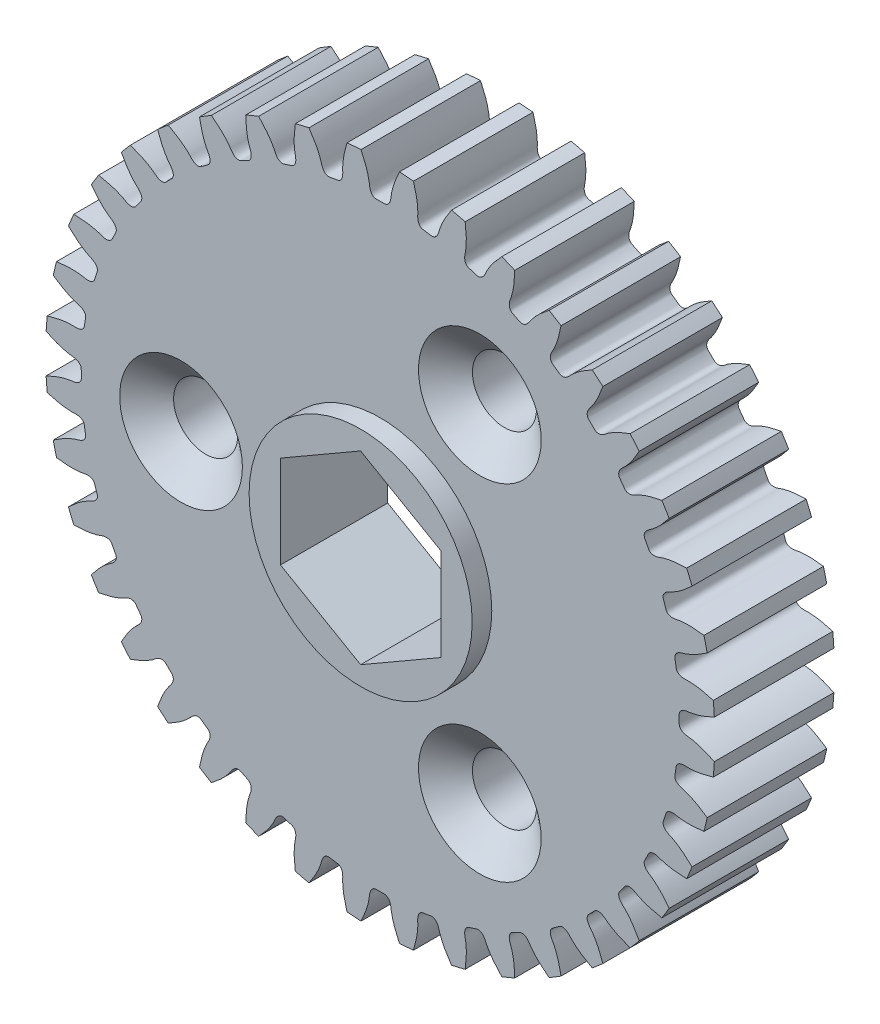
SolidWorks part; units mm, degrees
material "6061-T6 (SS)"
ref_plane "Front" through (0, 0, 0) normal (0, 0, 1) x (1, 0, 0)
ref_plane "Top" through (0, 0, 0) normal (0, 1, 0) x (1, 0, 0)
ref_plane "Side" through (0, 0, 0) normal (1, 0, 0) x (0, 0, -1)
ref_plane "Plane1" through (0, 0, -4.7625) normal (0, 0, -1) x (-1, 0, 0)
sketch "Sketch1" plane through (0, 0, -4.7625) normal (0, 0, -1) x (-1, 0, 0)
  arc A0 (-25.7968, 6.7684) -> (-26.058, 5.6808) centre (0, 0) ccw
  arc A1 (-26.5381, 2.6496) -> (-26.6258, 1.5345) centre (0, 0) ccw
  arc A2 (-26.6258, -1.5345) -> (-26.5381, -2.6496) centre (0, 0) ccw
  arc A3 (-26.058, -5.6808) -> (-25.7968, -6.7684) centre (0, 0) ccw
  arc A4 (-24.8485, -9.6872) -> (-24.4204, -10.7206) centre (0, 0) ccw
  arc A5 (-23.0271, -13.4551) -> (-22.4427, -14.4088) centre (0, 0) ccw
  arc A6 (-20.6388, -16.8917) -> (-19.9124, -17.7422) centre (0, 0) ccw
  arc A7 (-17.7422, -19.9124) -> (-16.8917, -20.6388) centre (0, 0) ccw
  arc A8 (-14.4088, -22.4427) -> (-13.4551, -23.0271) centre (0, 0) ccw
  arc A9 (-10.7206, -24.4204) -> (-9.6872, -24.8485) centre (0, 0) ccw
  arc A10 (-6.7684, -25.7968) -> (-5.6808, -26.058) centre (0, 0) ccw
  arc A11 (-2.6496, -26.5381) -> (-1.5345, -26.6258) centre (0, 0) ccw
  arc A12 (1.5345, -26.6258) -> (2.6496, -26.5381) centre (0, 0) ccw
  arc A13 (5.6808, -26.058) -> (6.7684, -25.7968) centre (0, 0) ccw
  arc A14 (9.6872, -24.8485) -> (10.7206, -24.4204) centre (0, 0) ccw
  arc A15 (13.4551, -23.0271) -> (14.4088, -22.4427) centre (0, 0) ccw
  arc A16 (16.8917, -20.6388) -> (17.7422, -19.9124) centre (0, 0) ccw
  arc A17 (19.9124, -17.7422) -> (20.6388, -16.8917) centre (0, 0) ccw
  arc A18 (22.4427, -14.4088) -> (23.0271, -13.4551) centre (0, 0) ccw
  arc A19 (24.4204, -10.7206) -> (24.8485, -9.6872) centre (0, 0) ccw
  arc A20 (25.7968, -6.7684) -> (26.058, -5.6808) centre (0, 0) ccw
  arc A21 (26.5381, -2.6496) -> (26.6258, -1.5345) centre (0, 0) ccw
  arc A22 (26.6258, 1.5345) -> (26.5381, 2.6496) centre (0, 0) ccw
  arc A23 (26.058, 5.6808) -> (25.7968, 6.7684) centre (0, 0) ccw
  arc A24 (24.8485, 9.6872) -> (24.4204, 10.7206) centre (0, 0) ccw
  arc A25 (23.0271, 13.4551) -> (22.4427, 14.4088) centre (0, 0) ccw
  arc A26 (20.6388, 16.8917) -> (19.9124, 17.7422) centre (0, 0) ccw
  arc A27 (17.7422, 19.9124) -> (16.8917, 20.6388) centre (0, 0) ccw
  arc A28 (14.4088, 22.4427) -> (13.4551, 23.0271) centre (0, 0) ccw
  arc A29 (10.7206, 24.4204) -> (9.6872, 24.8485) centre (0, 0) ccw
  arc A30 (6.7684, 25.7968) -> (5.6808, 26.058) centre (0, 0) ccw
  arc A31 (2.6496, 26.5381) -> (1.5345, 26.6258) centre (0, 0) ccw
  arc A32 (-1.5345, 26.6258) -> (-2.6496, 26.5381) centre (0, 0) ccw
  arc A33 (-5.6808, 26.058) -> (-6.7684, 25.7968) centre (0, 0) ccw
  arc A34 (-9.6872, 24.8485) -> (-10.7206, 24.4204) centre (0, 0) ccw
  arc A35 (-13.4551, 23.0271) -> (-14.4088, 22.4427) centre (0, 0) ccw
  arc A36 (-16.8917, 20.6388) -> (-17.7422, 19.9124) centre (0, 0) ccw
  arc A37 (-19.9124, 17.7422) -> (-20.6388, 16.8917) centre (0, 0) ccw
  arc A38 (-22.4427, 14.4088) -> (-23.0271, 13.4551) centre (0, 0) ccw
  arc A39 (-24.4204, 10.7206) -> (-24.8485, 9.6872) centre (0, 0) ccw
  spline S0 degree 3 number of poles 87 (-25.7968, 6.7684) -> (-24.8485, 9.6872)
  spline S1 degree 3 number of poles 87 (-26.5381, 2.6496) -> (-26.058, 5.6808)
  spline S2 degree 3 number of poles 87 (-26.6258, -1.5345) -> (-26.6258, 1.5345)
  spline S3 degree 3 number of poles 87 (-26.058, -5.6808) -> (-26.5381, -2.6496)
  spline S4 degree 3 number of poles 87 (-24.8485, -9.6872) -> (-25.7968, -6.7684)
  spline S5 degree 3 number of poles 87 (-23.0271, -13.4551) -> (-24.4204, -10.7206)
  spline S6 degree 3 number of poles 87 (-20.6388, -16.8917) -> (-22.4427, -14.4088)
  spline S7 degree 3 number of poles 87 (-17.7422, -19.9124) -> (-19.9124, -17.7422)
  spline S8 degree 3 number of poles 87 (-14.4088, -22.4427) -> (-16.8917, -20.6388)
  spline S9 degree 3 number of poles 87 (-10.7206, -24.4204) -> (-13.4551, -23.0271)
  spline S10 degree 3 number of poles 87 (-6.7684, -25.7968) -> (-9.6872, -24.8485)
  spline S11 degree 3 number of poles 87 (-2.6496, -26.5381) -> (-5.6808, -26.058)
  spline S12 degree 3 number of poles 87 (1.5345, -26.6258) -> (-1.5345, -26.6258)
  spline S13 degree 3 number of poles 87 (5.6808, -26.058) -> (2.6496, -26.5381)
  spline S14 degree 3 number of poles 87 (9.6872, -24.8485) -> (6.7684, -25.7968)
  spline S15 degree 3 number of poles 87 (13.4551, -23.0271) -> (10.7206, -24.4204)
  spline S16 degree 3 number of poles 87 (16.8917, -20.6388) -> (14.4088, -22.4427)
  spline S17 degree 3 number of poles 87 (19.9124, -17.7422) -> (17.7422, -19.9124)
  spline S18 degree 3 number of poles 87 (22.4427, -14.4088) -> (20.6388, -16.8917)
  spline S19 degree 3 number of poles 87 (24.4204, -10.7206) -> (23.0271, -13.4551)
  spline S20 degree 3 number of poles 87 (25.7968, -6.7684) -> (24.8485, -9.6872)
  spline S21 degree 3 number of poles 87 (26.5381, -2.6496) -> (26.058, -5.6808)
  spline S22 degree 3 number of poles 87 (26.6258, 1.5345) -> (26.6258, -1.5345)
  spline S23 degree 3 number of poles 87 (26.058, 5.6808) -> (26.5381, 2.6496)
  spline S24 degree 3 number of poles 87 (24.8485, 9.6872) -> (25.7968, 6.7684)
  spline S25 degree 3 number of poles 87 (23.0271, 13.4551) -> (24.4204, 10.7206)
  spline S26 degree 3 number of poles 87 (20.6388, 16.8917) -> (22.4427, 14.4088)
  spline S27 degree 3 number of poles 87 (17.7422, 19.9124) -> (19.9124, 17.7422)
  spline S28 degree 3 number of poles 87 (14.4088, 22.4427) -> (16.8917, 20.6388)
  spline S29 degree 3 number of poles 87 (10.7206, 24.4204) -> (13.4551, 23.0271)
  spline S30 degree 3 number of poles 87 (6.7684, 25.7968) -> (9.6872, 24.8485)
  spline S31 degree 3 number of poles 87 (2.6496, 26.5381) -> (5.6808, 26.058)
  spline S32 degree 3 number of poles 87 (-1.5345, 26.6258) -> (1.5345, 26.6258)
  spline S33 degree 3 number of poles 87 (-5.6808, 26.058) -> (-2.6496, 26.5381)
  spline S34 degree 3 number of poles 87 (-9.6872, 24.8485) -> (-6.7684, 25.7968)
  spline S35 degree 3 number of poles 87 (-13.4551, 23.0271) -> (-10.7206, 24.4204)
  spline S36 degree 3 number of poles 87 (-16.8917, 20.6388) -> (-14.4088, 22.4427)
  spline S37 degree 3 number of poles 87 (-19.9124, 17.7422) -> (-17.7422, 19.9124)
  spline S38 degree 3 number of poles 87 (-22.4427, 14.4088) -> (-20.6388, 16.8917)
  spline S39 degree 3 number of poles 87 (-24.4204, 10.7206) -> (-23.0271, 13.4551)
extrude "Boss-Extrude1" add sketch "Sketch1" against normal blind 9.525
sketch "Sketch3" plane through (0, 0, 4.7625) normal (0, 0, 1) x (1, 0, 0)
  circle A0 centre (0, 0) radius 8.89
extrude "Boss-Extrude3" add sketch "Sketch3" along normal blind 1.5621
sketch "Sketch4" plane through (0, 0, 6.3246) normal (0, 0, 1) x (1, 0, 0)
  line L0 (6.3881, -3.6882) -> (6.3881, 3.6882)
  line L1 (6.3881, 3.6882) -> (0, 7.3763)
  line L2 (0, 7.3763) -> (-6.3881, 3.6882)
  line L3 (-6.3881, 3.6882) -> (-6.3881, -3.6882)
  line L4 (-6.3881, -3.6882) -> (0, -7.3763)
  line L5 (0, -7.3763) -> (6.3881, -3.6882)
extrude "Cut-Extrude1" cut sketch "Sketch4" against normal through all
sketch "Sketch5" [suppressed] plane through (0, 0, 6.3246) normal (0, 0, 1) x (1, 0, 0)
  circle A0 centre (0, 0) radius 6.3881
  circle A1 centre (0, 0) radius 3.2004
  dimension "D1" = 12.7762
hole_wizard "CSK for #10 Flat Head Machine Screw (100)1" positions "Sketch7" profile "Sketch6" countersink size "#10" standard "ANSI Inch" end condition through all
sketch "Sketch7" plane through (0, 0, 4.7625) normal (0, 0, 1) x (1, 0, 0)
  line L4 (0, 0) -> (7.9375, 13.7482) construction
  line L6 (7.9375, -13.7482) -> (0, 0) construction
  line L9 (6.0979, 0) -> (-6.0979, 0) construction
  point P0 (-15.875, 0)
  point P2 (7.9375, 13.7482)
  point P4 (7.9375, -13.7482)
  dimension "D1" = 15.875
  dimension "D2" = 15.875
  dimension "D4" = 120
  dimension "D5" = 120
  dimension "D6" = 15.875
sketch "Sketch6" plane through (-15.875, 0, 4.7625) normal (1, 0, 0) x (0, -1, 0)
  line L0 (0, 0) -> (0, 9.525)
  line L1 (0, 9.525) -> (2.5527, 9.525)
  line L2 (2.5527, 9.525) -> (2.5527, 1.9608)
  line L3 (2.5527, 1.9608) -> (4.8895, 0)
  line L5 (4.8895, 0) -> (0, 0)
  line L6 (-2.5527, 1.9608) -> (-4.8895, 0) construction
  line L11 (0, -6.35) -> (0, 107.95) construction
  dimension "Thru Hole Dia." = 5.1054
  dimension "Thru Hole Depth" = 9.525
  dimension "Near C'Sink Dia." = 9.779
  dimension "Near C'Sink Angle" = 100
sketch "Sketch9" plane through (0, 0, -4.7625) normal (0, 0, -1) x (-1, 0, 0)
  circle A0 centre (0, 0) radius 12.319
  dimension "D1" = 24.638
extrude "Cut-Extrude2" cut sketch "Sketch9" against normal blind 2.54
sketch "Sketch10" plane through (0, 0, -4.7625) normal (0, 0, -1) x (-1, 0, 0)
  point P0 (-7.9375, 13.7482)
  point P1 (15.875, 0)
  point P3 (-7.9375, -13.7482)
